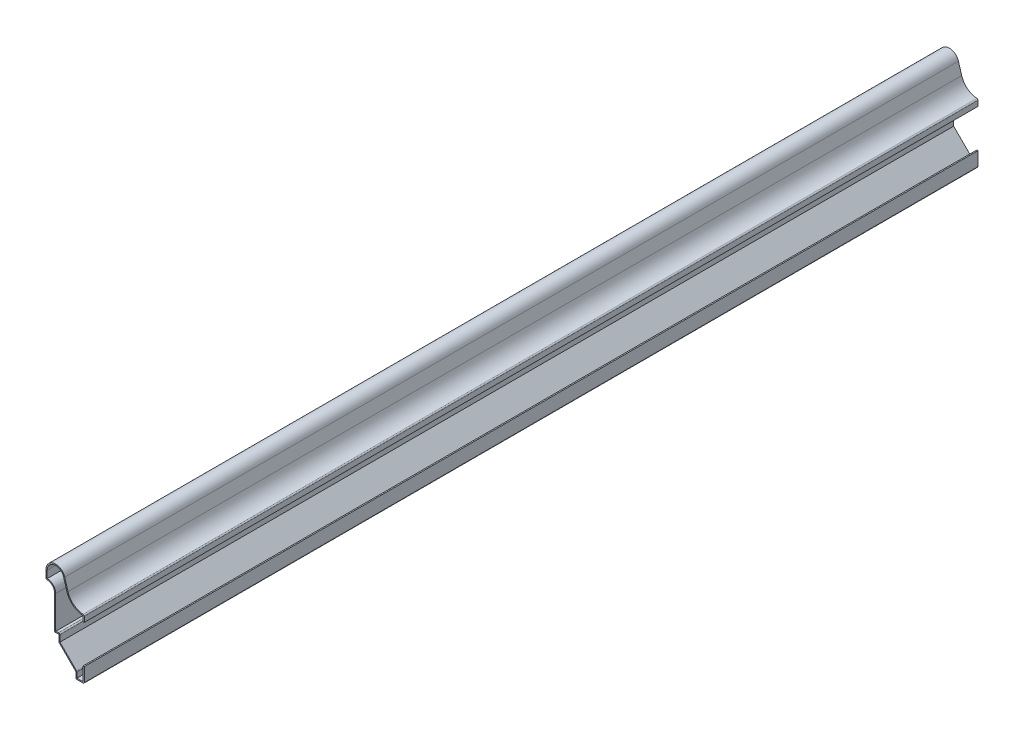
SolidWorks part; units mm, degrees
ref_plane "Front Plane" through (0, 0, 0) normal (0, 0, 1) x (1, 0, 0)
ref_plane "Top Plane" through (0, 0, 0) normal (0, 1, 0) x (1, 0, 0)
ref_plane "Right Plane" through (0, 0, 0) normal (1, 0, 0) x (0, 0, -1)
sketch "Sketch1" plane through (0, 0, 0) normal (0, 0, 1) x (1, 0, 0)
  line L0 (0, 11.1125) -> (0, 0)
  line L1 (0, 0) -> (-6.35, 0)
  line L2 (-6.35, 0) -> (-6.35, 4.7625)
  line L3 (-6.35, 4.7625) -> (-19.05, 17.4625)
  line L4 (-19.05, 17.4625) -> (-19.05, 22.6219)
  line L5 (-19.05, 22.6219) -> (-22.225, 22.225)
  line L6 (-22.225, 22.225) -> (-22.225, 47.682)
  line L7 (-28.575, 53.1812) -> (-28.575, 59.5312)
  line L8 (-14.5886, 61.5835) -> (-12.1646, 53.5015)
  line L9 (0, 44.45) -> (0, 39.6875)
  arc A0 (-22.225, 47.682) -> (-28.575, 53.1812) centre (-27.7812, 47.682) ccw
  arc A1 (-28.575, 59.5312) -> (-14.5886, 61.5835) centre (-21.4313, 59.5312) cw
  arc A2 (-12.1646, 53.5015) -> (0, 44.45) centre (0, 57.15) ccw
  point P17 (0, 0)
  point P19 (0, 0)
  point P20 (0, 57.1485)
  point P21 (0, 0)
  dimension "D14" = 5.5562
  dimension "D15" = 7.1437
  dimension "D16" = 12.7
  dimension "D1" = 28.575
  dimension "D2" = 66.675
  dimension "D3" = 13.4937
  dimension "D4" = 30.9562
  dimension "D5" = 0.3969
  dimension "D6" = 12.7
  dimension "D7" = 4.7625
  dimension "D8" = 11.1125
  dimension "D9" = 28.575
  dimension "D10" = 4.7625
  dimension "D11" = 6.35
  dimension "D12" = 12.7
  dimension "D13" = 6.35
extrude "Extrude-Thin1" add sketch "Sketch1" against normal blind 666.75 thin
fillet "Fillet1" radius 0.889 8 edges at (0, 0, -333.375) (-6.35, 0, -333.375) (-5.461, 5.1307, -333.375) (-19.05, 17.4625, -333.375) (-18.161, 23.6289, -333.375) (-22.225, 22.225, -333.375) (-28.575, 53.1812, -333.375) (0, 44.45, -333.375)
